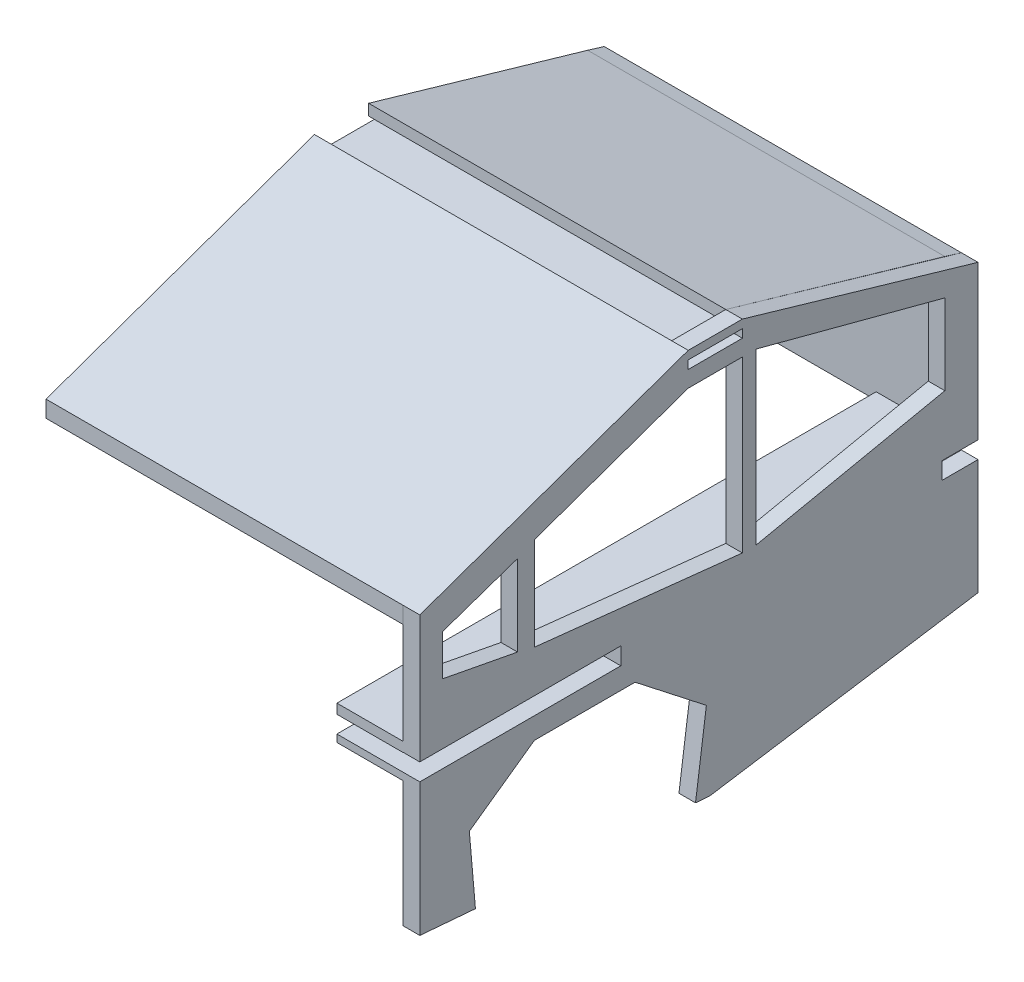
SolidWorks part; units mm, degrees
ref_plane "Front Plane" through (0, 0, 0) normal (0, 0, 1) x (1, 0, 0)
ref_plane "Top Plane" through (0, 0, 0) normal (0, 1, 0) x (1, 0, 0)
ref_plane "Right Plane" through (0, 0, 0) normal (1, 0, 0) x (0, 0, -1)
sketch "Sketch1" plane through (0, 0, 0) normal (1, 0, 0) x (0, 0, -1)
  line L7 (0, 117.5774) -> (159.1764, 117.5774) construction
  line L9 (-123.5256, 81.219) -> (-123.5256, 117.5774) construction
  line L11 (-123.5256, 117.5774) -> (-31.374, 117.5774) construction
  line L12 (159.1764, 71.351) -> (159.1764, 117.5774) construction
  line L22 (-123.5256, 81.219) -> (-123.5256, -25.0829)
  line L51 (5.2018, 40.001) -> (77.5282, 55.0563)
  line L52 (77.5282, 55.0563) -> (77.5282, 85.8304)
  line L55 (-123.5256, -25.0829) -> (-102.221, -26.86)
  line L56 (-102.221, -26.86) -> (-104.557, 0)
  line L57 (-104.557, 0) -> (-79.6468, 17.6863)
  line L58 (-79.6468, 17.6863) -> (-41.0945, 17.6863)
  line L59 (-41.0945, 17.6863) -> (-13.7798, -3.6413)
  line L60 (-13.7798, -3.6413) -> (-17.9475, -33.8894)
  line L61 (-17.9475, -33.8894) -> (-12.5619, -34.3386)
  line L67 (-79.6468, 84.2241) -> (-79.6468, 48.574)
  line L76 (-79.6468, 84.2241) -> (-20.7359, 105.0152)
  line L77 (-20.7359, 105.0152) -> (0, 105.0152)
  line L78 (0, 105.0152) -> (0, 40.0073)
  line L79 (5.2018, 40.001) -> (5.2018, 105.0152)
  line L80 (5.2018, 105.0152) -> (77.5282, 85.8304)
  line L81 (0, 40.0073) -> (-79.6468, 48.574)
  line L82 (-86.0905, 81.219) -> (-86.0905, 50.1978)
  line L85 (-86.0905, 81.219) -> (-114.76, 71.351)
  line L87 (-114.76, 71.351) -> (-114.76, 55.6667)
  line L88 (-114.76, 55.6667) -> (-86.0905, 50.1978)
  line L89 (-123.5256, 81.219) -> (-20.7359, 117.5774)
  line L93 (-20.7359, 111.2274) -> (0, 111.2274)
  line L94 (0, 111.2274) -> (0, 114.4024)
  line L97 (77.5282, 75.5815) -> (77.5282, 66.8423) construction
  line L100 (0, 117.5774) -> (90.2282, 91.2816)
  line L104 (90.2282, 59.8949) -> (90.2282, -12.9615) construction
  line L105 (-0.017, 117.4897) -> (159.1594, 71.2633) construction
  line L106 (90.2282, 91.2816) -> (90.2282, -18.3031)
  line L107 (-12.5789, -34.4263) -> (159.1594, -7.4926) construction
  line L108 (90.2282, -18.3031) -> (-12.5619, -34.3386)
  line L110 (-20.7359, 114.4024) -> (-20.7359, 111.2274) construction
  line L111 (-20.7359, 114.4024) -> (0, 114.4024)
  line L112 (-20.7359, 117.5774) -> (0, 117.5774)
  line L113 (-20.7359, 114.4024) -> (-20.7359, 111.2274)
  dimension "D1" = 3.175
  dimension "D2" = 6.35
  dimension "D4" = 20.7359
extrude "Boss-Extrude1" add sketch "Sketch1" along normal blind 6.35
sketch "Sketch2" plane through (6.35, 0, 0) normal (1, 0, 0) x (0, 0, -1)
  line L33 (-123.5256, 81.219) -> (-123.5256, -25.0829) construction
  line L38 (159.1764, -7.4049) -> (159.1764, 71.351) construction
  line L39 (159.1764, 25.8619) -> (76.5252, 25.8619)
  line L40 (159.1764, 25.8619) -> (159.1764, 32.3891)
  line L41 (159.1764, 32.3891) -> (76.5252, 32.3891)
  line L42 (76.5252, 25.8619) -> (76.5252, 32.3891)
  line L44 (-123.5256, 32.4659) -> (-123.5256, 25.8619)
  line L46 (-46.5558, 32.4659) -> (-46.5558, 25.8619)
  line L47 (-123.5256, 32.4659) -> (-46.5558, 32.4659)
  line L48 (-46.5558, 25.8619) -> (-123.5256, 25.8619)
  dimension "D3" = 6.5272
  dimension "D4" = 6.604
extrude "Cut-Extrude1" cut sketch "Sketch2" against normal through all
sketch "Sketch4" plane through (6.35, 0, 0) normal (1, 0, 0) x (0, 0, -1)
  line L1 (-123.5256, 81.2474) -> (-123.5256, -26.2693) construction
  line L2 (-123.5256, 35.1881) -> (158.7607, 35.1881)
  line L3 (-123.5256, 35.1881) -> (-123.5256, 23.3267)
  line L4 (-123.5256, 23.3267) -> (158.7607, 23.3267)
  line L5 (158.7607, 35.1881) -> (158.7607, 23.3267)
sketch "Sketch5" plane through (6.35, 0, 0) normal (1, 0, 0) x (0, 0, -1)
  line L2 (-0.017, 117.4897) -> (159.1594, 117.4897) construction
  line L4 (159.1594, -7.4926) -> (159.1594, 71.2633)
  line L5 (-123.5426, 81.1313) -> (-123.5426, 117.4897) construction
  line L6 (-123.5426, 117.4897) -> (-31.391, 117.4897) construction
  line L9 (159.1594, 71.2633) -> (159.1594, 117.4897) construction
  line L10 (-123.5426, 81.1313) -> (-123.5426, -25.1706)
  line L11 (5.1849, 39.9134) -> (77.5113, 54.9686)
  line L30 (77.5113, 54.9686) -> (77.5113, 85.7427)
  line L31 (-12.5789, -34.4263) -> (159.1594, -7.4926)
  line L32 (-123.5426, -25.1706) -> (-102.238, -26.9477)
  line L33 (-102.238, -26.9477) -> (-104.574, -0.0877)
  line L34 (-104.574, -0.0877) -> (-79.6638, 17.5986)
  line L35 (-79.6638, 17.5986) -> (-41.1115, 17.5986)
  line L36 (-41.1115, 17.5986) -> (-13.7968, -3.729)
  line L37 (-13.7968, -3.729) -> (-17.9645, -33.9771)
  line L38 (-17.9645, -33.9771) -> (-12.5789, -34.4263)
  line L39 (-79.6638, 84.1365) -> (-79.6638, 48.4864)
  line L40 (-79.6638, 84.1365) -> (-20.7529, 104.9275)
  line L41 (-20.7529, 104.9275) -> (-0.017, 104.9275)
  line L42 (-0.017, 104.9275) -> (-0.017, 39.9196)
  line L43 (5.1849, 39.9134) -> (5.1849, 104.9275)
  line L44 (5.1849, 104.9275) -> (77.5113, 85.7427)
  line L45 (-0.017, 39.9196) -> (-79.6638, 48.4864)
  line L46 (-86.1075, 81.1313) -> (-86.1075, 50.1101)
  line L47 (-86.1075, 81.1313) -> (-114.777, 71.2633)
  line L48 (-114.777, 71.2633) -> (-114.777, 55.579)
  line L49 (-114.777, 55.579) -> (-86.1075, 50.1101)
  line L50 (-123.5426, 81.1313) -> (-20.7529, 117.4897)
  line L51 (-0.017, 117.4897) -> (159.1594, 71.2633)
  line L52 (-20.7529, 117.4897) -> (-20.7529, 111.1397)
  line L53 (-20.7529, 111.1397) -> (-0.017, 111.1397)
  line L54 (-0.017, 111.1397) -> (-0.017, 117.4897)
  dimension "D1" = 6.35
sketch "Sketch6" plane through (0, 0, 0) normal (-1, 0, 0) x (0, 0, 1)
  line L0 (123.5256, 81.219) -> (123.5256, 32.4659) construction
  line L1 (-82.9764, 32.3891) -> (123.5256, 32.3891)
  line L3 (-82.9764, 36.1008) -> (123.5256, 36.1008)
  line L4 (123.5256, 32.3891) -> (123.5256, 36.1008)
  line L5 (123.5256, 25.8619) -> (123.5256, -25.0829) construction
  line L6 (-82.9764, 25.8619) -> (123.5256, 25.8619)
  line L8 (-82.9764, 23.0456) -> (123.5256, 23.0456)
  line L9 (123.5256, 25.8619) -> (123.5256, 23.0456)
  line L10 (-82.9764, 25.8619) -> (-82.9764, 23.0456)
  line L12 (-82.9764, 36.1008) -> (-82.9764, 32.3891)
extrude "Boss-Extrude3" add sketch "Sketch6" along normal blind 25.4
sketch "Sketch8" plane through (0, 0, 0) normal (-1, 0, 0) x (0, 0, 1)
  line L0 (0, 117.5774) -> (-83.8782, 93.2183)
  line L5 (0, 117.5774) -> (0.0112, 113.3442)
  line L7 (0.017, 111.1397) -> (20.7529, 111.1397)
  line L10 (123.5426, 81.1313) -> (123.5426, -25.1706) construction
  line L12 (123.5426, 74.869) -> (29.0978, 108.2701)
  line L22 (-9.5252, 108.4612) -> (29.0978, 108.2701)
  line L26 (123.5426, 74.869) -> (123.5256, 81.219)
  line L27 (123.5256, 81.219) -> (20.7359, 117.5774)
  line L30 (26.2283, 113.3442) -> (26.2283, 111.1397)
  line L33 (-83.8782, 93.2183) -> (-90.2282, 91.2816)
  line L34 (0.017, 117.4897) -> (-159.1594, 71.2633) construction
  line L35 (-90.2282, 32.3891) -> (-90.2282, 91.2816) construction
  line L36 (-90.2282, 91.2816) -> (-90.2282, 32.3891)
  line L38 (26.2283, 113.3442) -> (20.7529, 113.3442)
  line L40 (-90.2282, 32.3891) -> (-83.8782, 32.3891)
  line L41 (-90.2282, 32.3891) -> (-82.9764, 32.3891) construction
  line L43 (-83.8782, 93.2183) -> (-83.8782, 86.8683) construction
  line L44 (-83.8782, 32.3891) -> (-83.8782, 86.8683)
  line L45 (-83.8782, 86.8683) -> (-9.5252, 108.4612)
  line L46 (0.017, 111.1397) -> (-7.3776, 111.1397)
  line L47 (-7.3776, 111.1397) -> (-7.3776, 113.3442)
  line L48 (-7.3776, 113.3442) -> (0.0112, 113.3442)
  line L50 (26.2283, 111.1397) -> (20.7529, 111.1397)
  line L51 (20.7529, 117.4897) -> (20.7529, 111.1397) construction
  line L52 (20.7529, 113.3442) -> (20.7359, 117.5774)
  dimension "D1" = 6.35
  dimension "D2" = 6.35
extrude "Boss-Extrude5" add sketch "Sketch8" along normal blind 136.779
